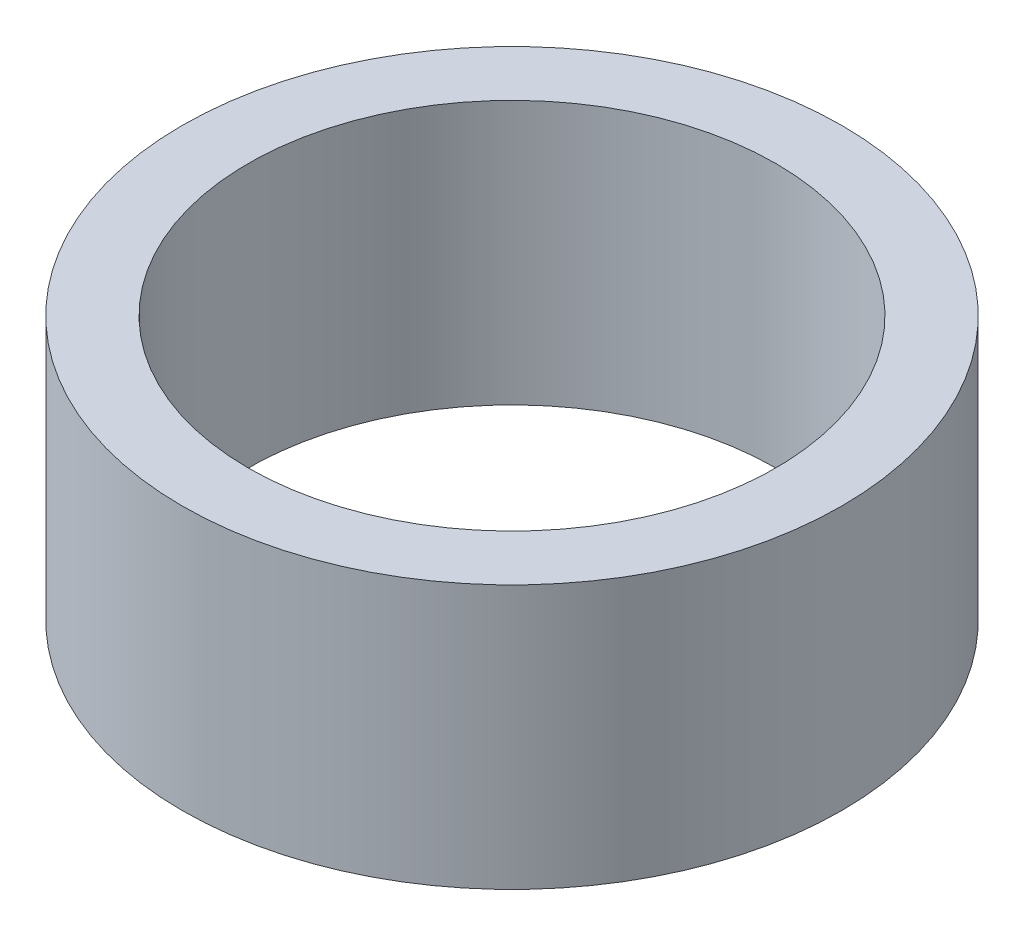
SolidWorks part; units mm, degrees
ref_plane "Plano frontal" through (0, 0, 0) normal (0, 0, 1) x (1, 0, 0)
ref_plane "Plano superior" through (0, 0, 0) normal (0, 1, 0) x (1, 0, 0)
ref_plane "Plano direito" through (0, 0, 0) normal (1, 0, 0) x (0, 0, -1)
sketch "Sketch3" plane through (0, 0, 0) normal (0, 1, 0) x (1, 0, 0)
  circle A0 centre (0, 0) radius 20
  circle A1 centre (0, 0) radius 25
extrude "Boss-Extrude1" add sketch "Sketch3" along normal blind 20
